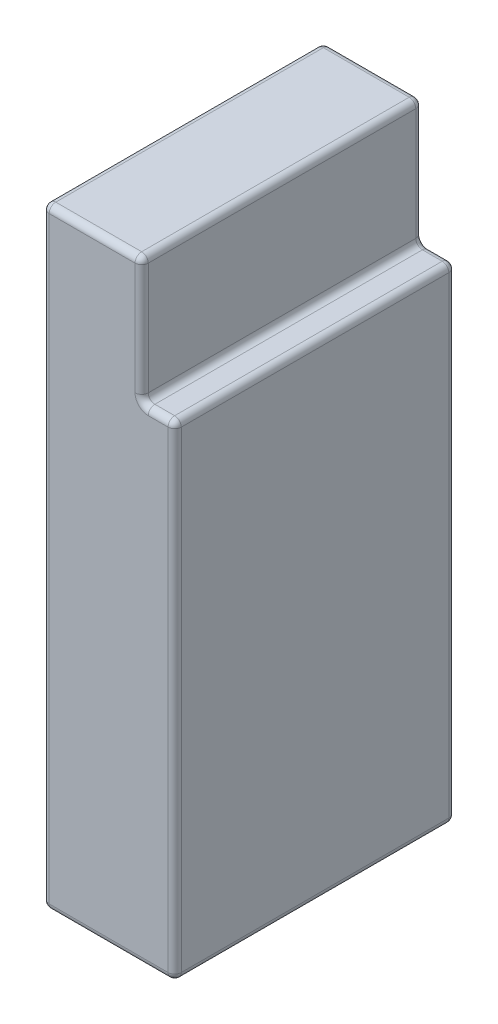
SolidWorks part; units mm, degrees
ref_plane "前视基准面" through (0, 0, 0) normal (0, 0, 1) x (1, 0, 0)
ref_plane "上视基准面" through (0, 0, 0) normal (0, 1, 0) x (1, 0, 0)
ref_plane "右视基准面" through (0, 0, 0) normal (1, 0, 0) x (0, 0, -1)
other "Configuration Table"
sketch "草图1" plane through (0, 0, 0) normal (0, 1, 0) x (1, 0, 0)
  line L1 (-10, -21.25) -> (10, -21.25)
  line L2 (-10, -21.25) -> (-10, 21.25)
  line L3 (-10, 21.25) -> (10, 21.25)
  line L4 (10, -21.25) -> (10, 21.25)
  line L5 (-10, -21.25) -> (10, 21.25) construction
  line L6 (-10, 21.25) -> (10, -21.25) construction
  point P0 (0, 0)
  dimension "D1" = 20
  dimension "D2" = 42.5
extrude "凸台-拉伸1" add sketch "草图1" along normal blind 92.5
sketch "草图3" plane through (10, 0, 0) normal (1, 0, 0) x (0, 0, -1)
  line L0 (21.25, 92.5) -> (21.25, 0) construction
  line L1 (-21.25, 92.5) -> (21.25, 92.5)
  line L2 (-21.25, 92.5) -> (-21.25, 73.5)
  line L3 (-21.25, 73.5) -> (21.25, 73.5)
  line L4 (21.25, 92.5) -> (21.25, 73.5)
  dimension "D1" = 19
extrude "切除-拉伸1" cut sketch "草图3" against normal blind 5
fillet "圆角1" radius 1 18 edges at (-2.5, 92.5, -21.25) (0, 0, -21.25) (7.5, 73.5, -21.25) (-10, 46.25, -21.25) (-10, 92.5, 0) (-10, 0, 0) (0, 0, 21.25) (-10, 46.25, 21.25) (-2.5, 92.5, 21.25) (7.5, 73.5, 21.25) (5, 92.5, 0) (5, 83, -21.25) (5, 73.5, 0) (5, 83, 21.25) (10, 0, 0) (10, 36.75, 21.25) (10, 73.5, 0) (10, 36.75, -21.25)
